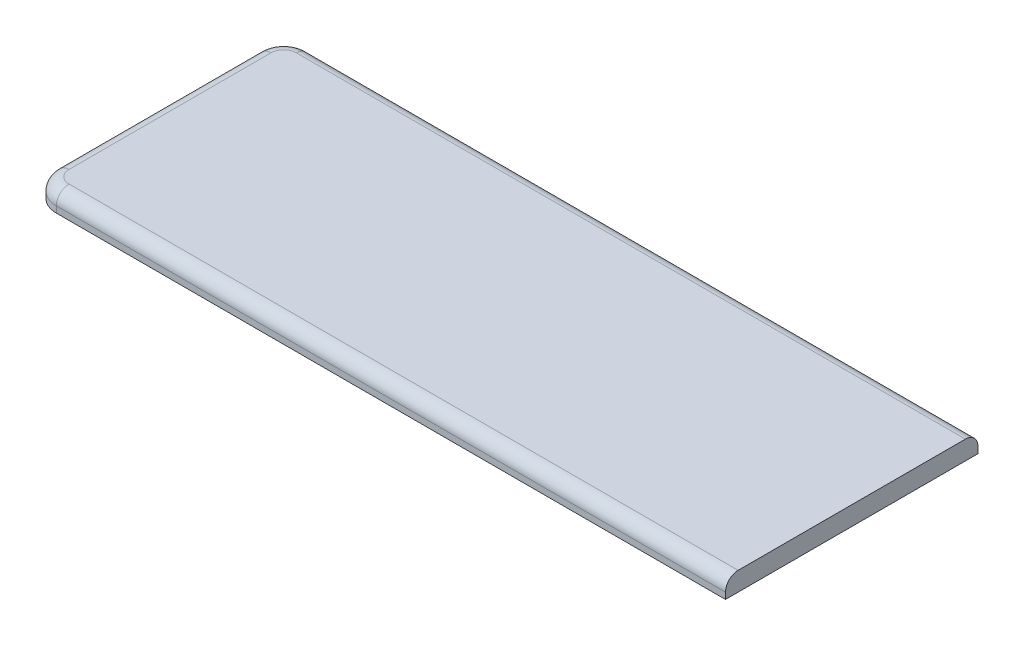
SolidWorks part; units mm, degrees
ref_plane "Front Plane" through (0, 0, 0) normal (0, 0, 1) x (1, 0, 0)
ref_plane "Top Plane" through (0, 0, 0) normal (0, 1, 0) x (1, 0, 0)
ref_plane "Right Plane" through (0, 0, 0) normal (1, 0, 0) x (0, 0, -1)
sketch "Sketch1" plane through (0, 0, 0) normal (0, 1, 0) x (1, 0, 0)
  line L1 (69.85, -25.4) -> (-69.85, -25.4)
  line L2 (69.85, -25.4) -> (69.85, 25.4)
  line L3 (69.85, 25.4) -> (-69.85, 25.4)
  line L4 (-69.85, -25.4) -> (-69.85, 25.4)
  line L5 (69.85, -25.4) -> (-69.85, 25.4) construction
  line L6 (69.85, 25.4) -> (-69.85, -25.4) construction
  point P0 (0, 0)
  dimension "D1" = 139.7
  dimension "D2" = 50.8
extrude "Boss-Extrude1" add sketch "Sketch1" along normal blind 3.81
fillet "Fillet4" radius 5.08 2 edges at (-69.85, 1.905, -25.4) (-69.85, 1.905, 25.4)
fillet "Fillet5" radius 2.54 5 edges at (2.54, 3.81, -25.4) (-68.3621, 3.81, -23.9121) (-69.85, 3.81, 0) (-68.3621, 3.81, 23.9121) (2.54, 3.81, 25.4)
